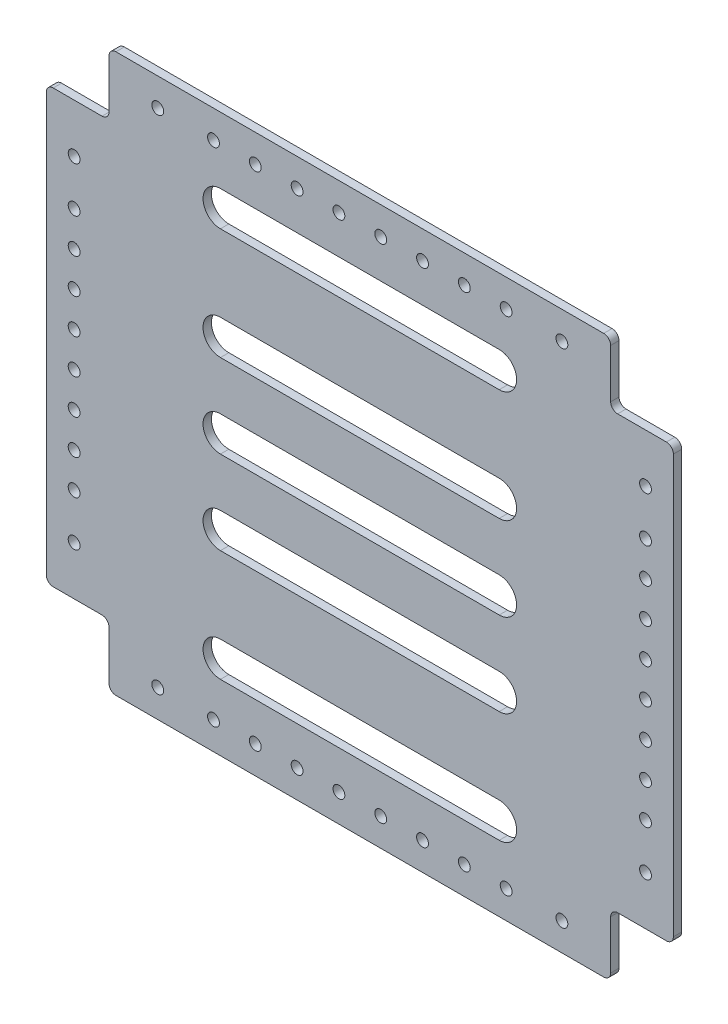
SolidWorks part; units mm, degrees
material "6061-T6 (SS)"
ref_plane "前视基准面" through (0, 0, 0) normal (0, 0, 1) x (1, 0, 0)
ref_plane "上视基准面" through (0, 0, 0) normal (0, 1, 0) x (1, 0, 0)
ref_plane "右视基准面" through (0, 0, 0) normal (1, 0, 0) x (0, 0, -1)
sketch "草图1" plane through (0, 0, 0) normal (0, 0, 1) x (1, 0, 0)
  line L1 (225, -200) -> (-225, -200)
  line L2 (225, -200) -> (225, 200)
  line L3 (225, 200) -> (-225, 200)
  line L4 (-225, -200) -> (-225, 200)
  line L5 (225, -200) -> (-225, 200) construction
  line L6 (225, 200) -> (-225, -200) construction
  line L7 (115, -100) -> (-115, -100) construction
  line L8 (115, -100) -> (115, 100) construction
  line L9 (115, 100) -> (-115, 100) construction
  line L10 (-115, -100) -> (-115, 100) construction
  line L11 (115, -100) -> (-115, 100) construction
  line L12 (115, 100) -> (-115, -100) construction
  circle A0 centre (-115, 100) radius 3.25 construction
  circle A1 centre (115, 100) radius 3.25 construction
  circle A2 centre (115, -100) radius 3.25 construction
  circle A3 centre (-115, -100) radius 3.25 construction
  point P0 (0, 0)
  point P6 (0, 0)
  dimension "D5" = 6.5
  dimension "D6" = 6.5
  dimension "D7" = 6.5
  dimension "D8" = 6.5
  dimension "D1" = 450
  dimension "D2" = 400
  dimension "D3" = 200
  dimension "D4" = 230
extrude "凸台-拉伸1" add sketch "草图1" along normal blind 6
sketch "草图3" plane through (0, 0, 6) normal (0, 0, 1) x (1, 0, 0)
  line L0 (225, -200) -> (225, 200) construction
  line L1 (-225, -200) -> (225, -200) construction
  line L2 (205, -180) -> (205, -120) construction
  line L3 (145, -180) -> (205, -180) construction
  line L4 (0, 200) -> (0, 0) construction
  line L5 (225, 200) -> (-225, 200) construction
  line L6 (0, 0) -> (-225, 0) construction
  line L7 (-225, 200) -> (-225, -200) construction
  line L8 (145, 180) -> (205, 180) construction
  line L9 (205, 180) -> (205, 120) construction
  line L10 (-205, 180) -> (-205, 120) construction
  line L11 (-145, 180) -> (-205, 180) construction
  line L12 (-145, -180) -> (-205, -180) construction
  line L13 (-205, -180) -> (-205, -120) construction
  circle A0 centre (205, -180) radius 3.75
  circle A1 centre (205, -120) radius 4.25
  circle A2 centre (145, -180) radius 4.25
  circle A3 centre (145, 180) radius 4.25
  circle A4 centre (205, 120) radius 4.25
  circle A5 centre (205, 180) radius 3.75
  circle A6 centre (-205, 180) radius 3.75
  circle A7 centre (-205, 120) radius 4.25
  circle A8 centre (-145, 180) radius 4.25
  circle A9 centre (-145, -180) radius 4.25
  circle A10 centre (-205, -120) radius 4.25
  circle A11 centre (-205, -180) radius 3.75
  dimension "D1" = 7.5
  dimension "D2" = 20
  dimension "D3" = 20
  dimension "D4" = 8.5
  dimension "D5" = 60
  dimension "D6" = 8.5
  dimension "D7" = 60
extrude "切除-拉伸2" cut sketch "草图3" against normal blind 50
sketch "草图4" plane through (0, 0, 6) normal (0, 0, 1) x (1, 0, 0)
  line L0 (225, 0) -> (0, 0) construction
  line L1 (225, -200) -> (225, 200) construction
  line L2 (0, -200) -> (0, 200) construction
  line L3 (225, 200) -> (-225, 200) construction
  line L4 (100, 0) -> (-100, 0) construction
  line L5 (100, -12.5) -> (-100, -12.5)
  line L6 (100, 12.5) -> (-100, 12.5)
  line L7 (100, 60) -> (-100, 60) construction
  line L8 (100, 47.5) -> (-100, 47.5)
  line L9 (100, 72.5) -> (-100, 72.5)
  line L10 (100, -60) -> (-100, -60) construction
  line L11 (100, -47.5) -> (-100, -47.5)
  line L12 (100, -72.5) -> (-100, -72.5)
  line L13 (100, 140) -> (-100, 140) construction
  line L14 (100, 127.5) -> (-100, 127.5)
  line L15 (100, 152.5) -> (-100, 152.5)
  line L16 (100, -140) -> (-100, -140) construction
  line L17 (100, -127.5) -> (-100, -127.5)
  line L18 (100, -152.5) -> (-100, -152.5)
  arc A0 (100, -12.5) -> (100, 12.5) centre (100, 0) ccw
  arc A1 (-100, 12.5) -> (-100, -12.5) centre (-100, 0) ccw
  arc A2 (100, 47.5) -> (100, 72.5) centre (100, 60) ccw
  arc A3 (-100, 72.5) -> (-100, 47.5) centre (-100, 60) ccw
  arc A4 (100, -47.5) -> (100, -72.5) centre (100, -60) cw
  arc A5 (-100, -72.5) -> (-100, -47.5) centre (-100, -60) cw
  arc A6 (100, 127.5) -> (100, 152.5) centre (100, 140) ccw
  arc A7 (-100, 152.5) -> (-100, 127.5) centre (-100, 140) ccw
  arc A8 (100, -127.5) -> (100, -152.5) centre (100, -140) cw
  arc A9 (-100, -152.5) -> (-100, -127.5) centre (-100, -140) cw
  point P10 (0, 0)
  point P19 (0, 60)
  point P25 (0, -60)
  point P32 (0, 140)
  point P39 (0, -140)
  dimension "D2" = 200
  dimension "D1" = 25
  dimension "D4" = 60
  dimension "D6" = 80
  dimension "D3" = 2
  dimension "D5" = 2
extrude "切除-拉伸3" cut sketch "草图4" against normal blind 50
sketch "草图5" plane through (0, 0, 6) normal (0, 0, 1) x (1, 0, 0)
  line L0 (0, 0) -> (253.0998, 0) construction
  line L1 (225, -200) -> (180, -200)
  line L2 (225, -200) -> (225, -155)
  line L3 (225, -155) -> (180, -155)
  line L4 (180, -200) -> (180, -155)
  line L5 (202.5, -155) -> (202.5, -200) construction
  line L6 (225, -177.5) -> (180, -177.5) construction
  line L7 (0, 0) -> (0, 234.088) construction
  line L8 (-225, -177.5) -> (-180, -177.5) construction
  line L9 (-202.5, -155) -> (-202.5, -200) construction
  line L10 (-180, -200) -> (-180, -155)
  line L11 (-225, -155) -> (-180, -155)
  line L12 (-225, -200) -> (-225, -155)
  line L13 (-225, -200) -> (-180, -200)
  line L14 (-202.5, 155) -> (-202.5, 200) construction
  line L15 (-225, 177.5) -> (-180, 177.5) construction
  line L16 (225, 177.5) -> (180, 177.5) construction
  line L17 (202.5, 155) -> (202.5, 200) construction
  line L18 (-225, 200) -> (-180, 200)
  line L19 (-225, 200) -> (-225, 155)
  line L20 (-225, 155) -> (-180, 155)
  line L21 (-180, 200) -> (-180, 155)
  line L22 (180, 200) -> (180, 155)
  line L23 (225, 155) -> (180, 155)
  line L24 (225, 200) -> (225, 155)
  line L25 (225, 200) -> (180, 200)
  point P15 (-202.5, -177.5)
  point P32 (202.5, 177.5)
  point P33 (-202.5, 177.5)
  point P52 (202.5, -177.5)
  dimension "D1" = 45
  dimension "D2" = 45
extrude "切除-拉伸4" cut sketch "草图5" against normal blind 56
fillet "圆角1" radius 5 12 edges at (180, 200, 3) (-180, 155, 3) (-225, -155, 3) (-180, -155, 3) (-180, -200, 3) (180, -200, 3) (180, -155, 3) (225, -155, 3) (225, 155, 3) (180, 155, 3) (-225, 155, 3) (-180, 200, 3)
sketch "草图6" plane through (0, 0, 0) normal (0, 0, -1) x (-1, 0, 0)
  line L0 (0, 0) -> (-225, 0) construction
  line L1 (-225, -150) -> (-225, 150) construction
  line L2 (0, 200) -> (0, -200) construction
  line L3 (175, -200) -> (-175, -200) construction
  line L4 (145, -180) -> (-145, -180) construction
  line L5 (-205, -120) -> (-205, 120) construction
  line L6 (145, 180) -> (-145, 180) construction
  circle A0 centre (15, -180) radius 4.25
  circle A1 centre (45, -180) radius 4.25
  circle A2 centre (75, -180) radius 4.25
  circle A3 centre (105, -180) radius 4.25
  circle A4 centre (-105, -180) radius 4.25
  circle A5 centre (-75, -180) radius 4.25
  circle A6 centre (-45, -180) radius 4.25
  circle A7 centre (-15, -180) radius 4.25
  circle A8 centre (-15, 180) radius 4.25
  circle A9 centre (-45, 180) radius 4.25
  circle A10 centre (-75, 180) radius 4.25
  circle A11 centre (-105, 180) radius 4.25
  circle A12 centre (105, 180) radius 4.25
  circle A13 centre (75, 180) radius 4.25
  circle A14 centre (45, 180) radius 4.25
  circle A15 centre (15, 180) radius 4.25
  circle A16 centre (-205, -12.5) radius 4.25
  circle A17 centre (-205, -37.5) radius 4.25
  circle A18 centre (-205, -62.5) radius 4.25
  circle A19 centre (-205, -87.5) radius 4.25
  circle A20 centre (-205, 87.5) radius 4.25
  circle A21 centre (-205, 62.5) radius 4.25
  circle A22 centre (-205, 37.5) radius 4.25
  circle A23 centre (-205, 12.5) radius 4.25
  circle A24 centre (205, 12.5) radius 4.25
  circle A25 centre (205, 37.5) radius 4.25
  circle A26 centre (205, 62.5) radius 4.25
  circle A27 centre (205, 87.5) radius 4.25
  circle A28 centre (205, -87.5) radius 4.25
  circle A29 centre (205, -62.5) radius 4.25
  circle A30 centre (205, -37.5) radius 4.25
  circle A31 centre (205, -12.5) radius 4.25
  dimension "D1" = 8.5
  dimension "D2" = 30
  dimension "D4" = 30
  dimension "D5" = 8.5
  dimension "D6" = 25
  dimension "D8" = 25
  dimension "D3" = 4
  dimension "D7" = 4
extrude "切除-拉伸5" cut sketch "草图6" against normal blind 90
